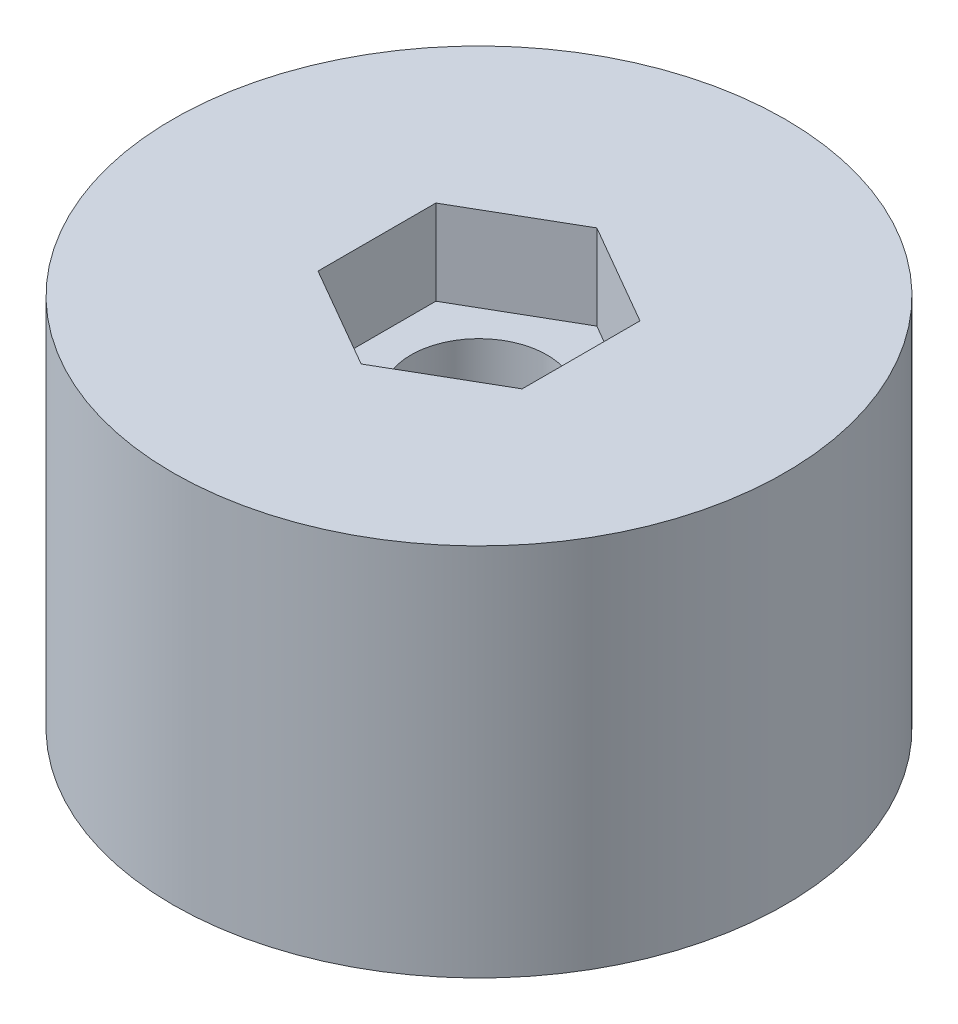
SolidWorks part; units mm, degrees
ref_plane "Front Plane" through (0, 0, 0) normal (0, 0, 1) x (1, 0, 0)
ref_plane "Top Plane" through (0, 0, 0) normal (0, 1, 0) x (1, 0, 0)
ref_plane "Right Plane" through (0, 0, 0) normal (1, 0, 0) x (0, 0, -1)
sketch "Sketch1" plane through (0, 0, 0) normal (0, 1, 0) x (1, 0, 0)
  circle A0 centre (0, 0) radius 9
  dimension "D1" = 18
extrude "Boss-Extrude1" add sketch "Sketch1" along normal blind 11
sketch "Sketch2" plane through (0, 11, 0) normal (0, 1, 0) x (1, 0, 0)
  circle A0 centre (0, 0) radius 2
  dimension "D1" = 4
extrude "Cut-Extrude1" cut sketch "Sketch2" against normal up to next
sketch "Sketch3" plane through (0, 11, 0) normal (0, 1, 0) x (1, 0, 0)
  line L1 (3, -1.7321) -> (3, 1.7321)
  line L2 (3, 1.7321) -> (0, 3.4641)
  line L3 (0, 3.4641) -> (-3, 1.7321)
  line L4 (-3, 1.7321) -> (-3, -1.7321)
  line L5 (-3, -1.7321) -> (0, -3.4641)
  line L6 (0, -3.4641) -> (3, -1.7321)
  circle A0 centre (0, 0) radius 3 construction
  dimension "D1" = 6
extrude "Cut-Extrude2" cut sketch "Sketch3" against normal blind 2.5
